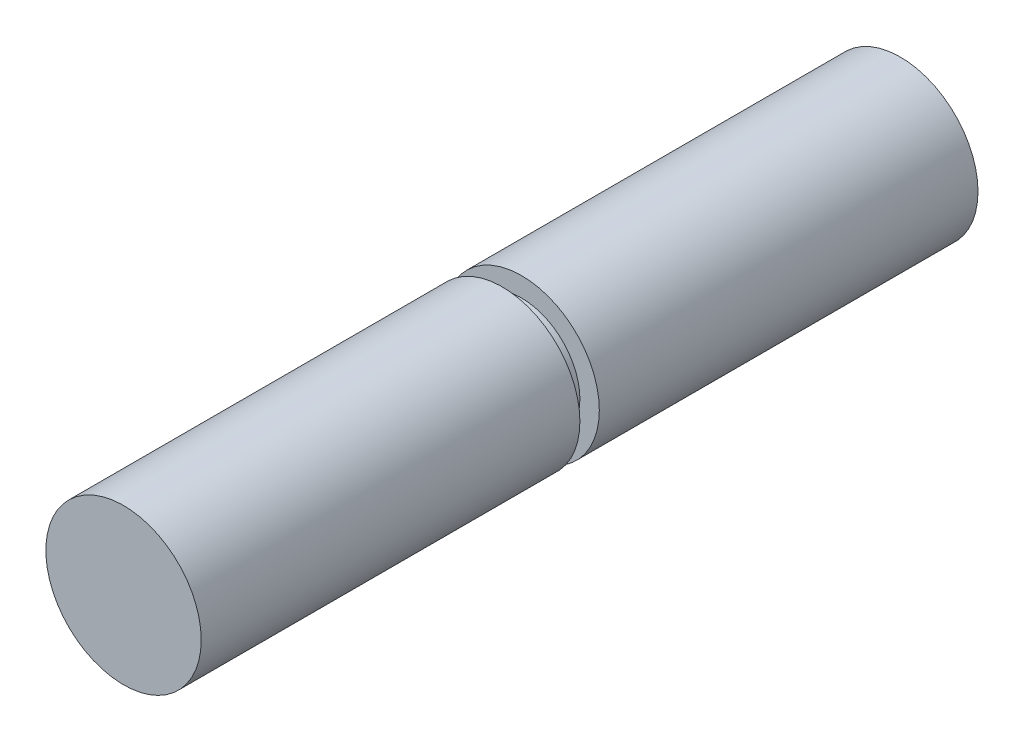
SolidWorks part; units mm, degrees
ref_plane "Front Plane" through (0, 0, 0) normal (0, 0, 1) x (1, 0, 0)
ref_plane "Top Plane" through (0, 0, 0) normal (0, 1, 0) x (1, 0, 0)
ref_plane "Right Plane" through (0, 0, 0) normal (1, 0, 0) x (0, 0, -1)
sketch "Sketch1" plane through (0, 0, 0) normal (0, 0, 1) x (1, 0, 0)
  circle A0 centre (0, 0) radius 25.4
  dimension "D1" = 50.8
extrude "Boss-Extrude1" add sketch "Sketch1" along normal mid plane 254
sketch "Sketch2" plane through (0, 0, 0) normal (1, 0, 0) x (0, 0, -1)
  line L0 (0, -49.6387) -> (0, 63.3346) construction
  line L2 (-3.175, 25.4) -> (3.175, 25.4)
  line L3 (-3.175, 25.4) -> (-3.175, 19.05)
  line L4 (-3.175, 19.05) -> (3.175, 19.05)
  line L5 (3.175, 25.4) -> (3.175, 19.05)
  line L6 (-3.175, 25.4) -> (3.175, 19.05) construction
  line L7 (-3.175, 19.05) -> (3.175, 25.4) construction
  point P3 (0, 22.225)
  dimension "D1" = 6.35
  dimension "D2" = 6.35
  dimension "D3" = 19.05
revolve "Cut-Revolve1" cut sketch "Sketch2" angle 360 about axis through (0, 0, 127) along (0, 0, -1)
